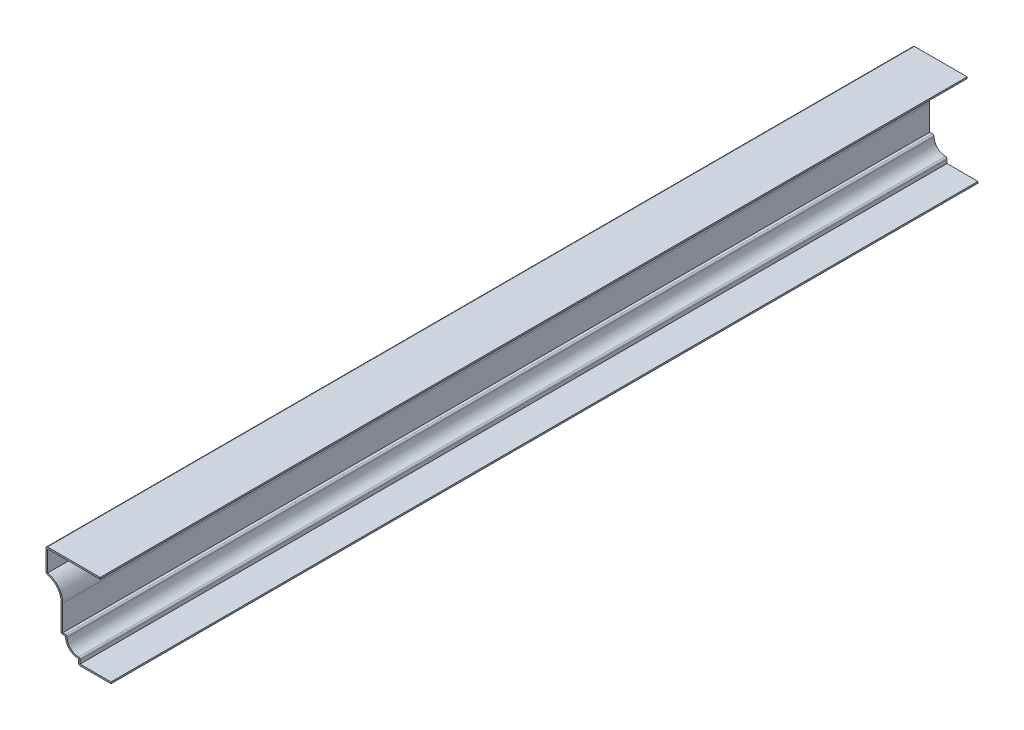
SolidWorks part; units mm, degrees
ref_plane "Front Plane" through (0, 0, 0) normal (0, 0, 1) x (1, 0, 0)
ref_plane "Top Plane" through (0, 0, 0) normal (0, 1, 0) x (1, 0, 0)
ref_plane "Right Plane" through (0, 0, 0) normal (1, 0, 0) x (0, 0, -1)
sketch "Sketch1" plane through (0, 0, 0) normal (0, 0, 1) x (1, 0, 0)
  line L0 (0, 0) -> (-23.8125, 0)
  line L1 (-23.8125, 0) -> (-23.8125, 3.9687)
  line L2 (-33.3375, 13.4937) -> (-36.5125, 13.4937)
  line L3 (-36.5125, 13.4937) -> (-36.5125, 33.4371)
  line L4 (-47.625, 46.0375) -> (-47.625, 63.5)
  line L5 (-47.625, 63.5) -> (-7.9375, 63.5)
  arc A0 (-23.8125, 3.9687) -> (-33.3375, 13.4937) centre (-23.8125, 13.4937) cw
  arc A1 (-36.5125, 33.4371) -> (-47.625, 46.0375) centre (-49.2125, 33.4371) ccw
  dimension "D6" = 9.525
  dimension "D10" = 12.7
  dimension "D1" = 63.5
  dimension "D2" = 47.625
  dimension "D3" = 39.6875
  dimension "D4" = 23.8125
  dimension "D5" = 3.9688
  dimension "D7" = 9.525
  dimension "D8" = 3.175
  dimension "D9" = 32.5437
  dimension "D11" = 17.4625
extrude "Extrude-Thin1" add sketch "Sketch1" against normal blind 635 thin
fillet "Fillet1" radius 1.143 6 edges at (-23.8125, 0, -317.5) (-22.6695, 5.19, -317.5) (-32.1162, 14.6367, -317.5) (-36.5125, 13.4937, -317.5) (-47.625, 46.0375, -317.5) (-47.625, 63.5, -317.5)
